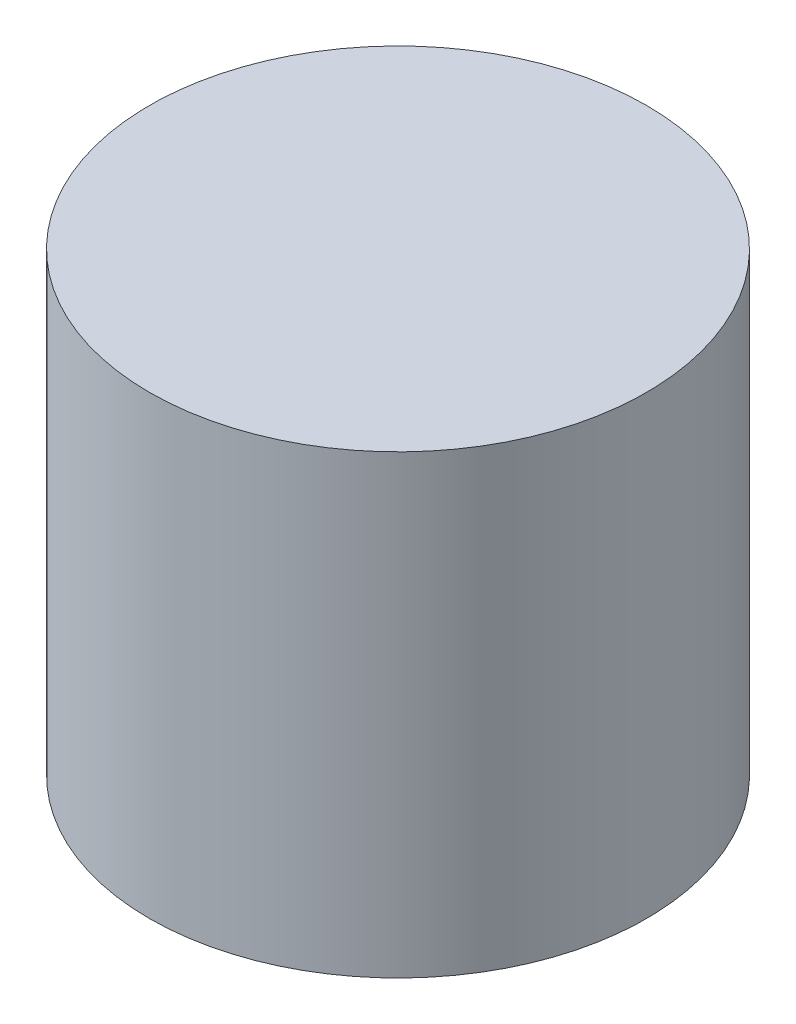
SolidWorks part; units mm, degrees
ref_plane "Front Plane" through (0, 0, 0) normal (0, 0, 1) x (1, 0, 0)
ref_plane "Top Plane" through (0, 0, 0) normal (0, 1, 0) x (1, 0, 0)
ref_plane "Right Plane" through (0, 0, 0) normal (1, 0, 0) x (0, 0, -1)
sketch "Sketch1" plane through (0, 0, 0) normal (0, 1, 0) x (1, 0, 0)
  circle A0 centre (0, 0) radius 6
  dimension "D1" = 12
extrude "Boss-Extrude1" add sketch "Sketch1" along normal blind 11
